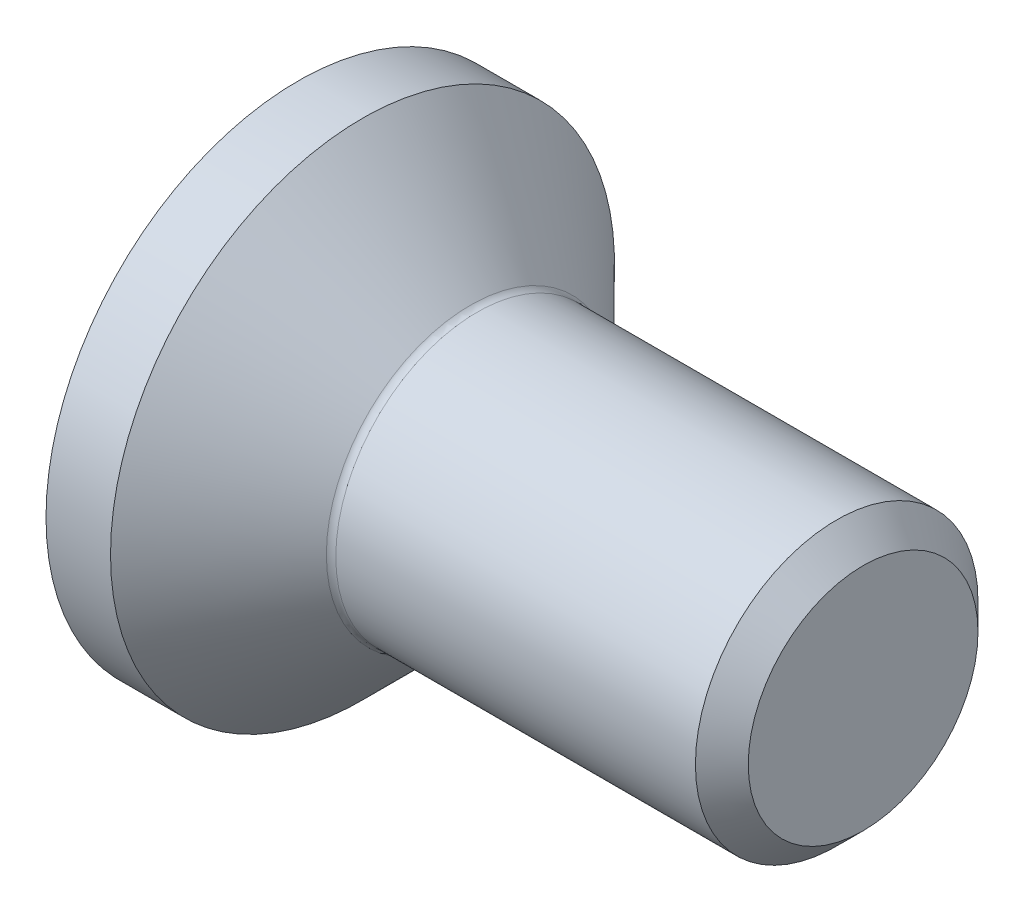
SolidWorks part; units mm, degrees
ref_plane "Plane1" through (0, 0, 0) normal (0, 0, 1) x (1, 0, 0)
ref_plane "Plane2" through (0, 0, 0) normal (0, 1, 0) x (1, 0, 0)
ref_plane "Plane3" through (0, 0, 0) normal (1, 0, 0) x (0, 0, -1)
revolve "BaseBody" add sketch "BodySke" angle 360 about L6
sketch "BodySke" plane through (0, 0, 0) normal (0, 0, 1) x (1, 0, 0)
  line L0 (0, 0) -> (0, 2.675)
  line L1 (0.685, 2.675) -> (1.86, 1.5)
  line L2 (0, 2.675) -> (0.685, 2.675)
  line L3 (1.86, 1.5) -> (5.7195, 1.5)
  line L4 (6, 1.2195) -> (6, 0)
  line L5 (6, 0) -> (0, 0)
  line L6 (0, 0) -> (127, 0) construction
  line L7 (0.685, -2.675) -> (1.86, -1.5) construction
  line L8 (6, 1.2195) -> (5.7195, 1.5)
  line L9 (0, -2.675) -> (0.685, -2.675) construction
  line L10 (6, -1.2195) -> (5.7195, -1.5) construction
  line L11 (2.36, 7.85) -> (2.36, -14.375) construction
  line L12 (0, 19.05) -> (0, -3.175) construction
  dimension "D1" = 0.685
  dimension "Diameter" = 3
  dimension "Head_ht" = 1.86
  dimension "Length" = 6
  dimension "Body_ch_ang" = 45
  dimension "Head_dia" = 5.35
  dimension "Minor_dia" = 2.439
  dimension "Head_ang" = 90
  dimension "Advance" = 0.5
  dimension "Thread_nom" = 6
cosmetic thread "ThreadCosmetic" [suppressed] parameters "Thread_length"=3.14, "Thread_minor"=2.439
fillet "Fillet1" radius 0.1 1 edges at (1.86, 0, 1.5)
sketch "Sketch2" plane through (0, 0, 0) normal (0, 0, 1) x (1, 0, 0)
  line L0 (0, 1) -> (1.1, 1)
  line L1 (1.1, 1) -> (1.6774, 0)
  line L2 (0, 0) -> (127, 0) construction
  line L3 (1.6774, 0) -> (0, 0)
  line L4 (0, 0) -> (0, 1)
  line L5 (0, -1) -> (1.1, -1) construction
  line L6 (0, 0) -> (47.625, 0) construction
  line L8 (0, 2.675) -> (0, -2.675) construction
  dimension "D2" = 60
  dimension "PreBroach_depth" = 1.1
  dimension "PreBroach_dia" = 2
revolve "PreBroach" cut sketch "Sketch2" angle 360 about L6
sketch "Sketch3" plane through (0, 0, 0) normal (-1, 0, 0) x (0, 0, 1)
  line L0 (-1, -0.5774) -> (-1, 0.5774)
  line L1 (-1, 0.5774) -> (0, 1.1547)
  line L2 (0, 1.1547) -> (1, 0.5774)
  line L3 (1, 0.5774) -> (1, -0.5774)
  line L4 (1, -0.5774) -> (0, -1.1547)
  line L5 (0, -1.1547) -> (-1, -0.5774)
  dimension "D1" = 1
  dimension "D2" = 1
  dimension "D3" = 2
  dimension "Hex_size" = 2
extrude "Hex" cut sketch "Sketch3" against normal blind 1.1
sketch "ThdSchSke" plane through (0, 0, 0) normal (0, 0, 1) x (1, 0, 0)
  line L0 (2.86, -1.2195) -> (2.6636, -1.5)
  line L1 (2.86, -1.2195) -> (3.0564, -1.5)
  line L2 (3.0564, -1.5) -> (3.0564, -1.875)
  line L3 (-3.175, 0) -> (5.1513, 0) construction
  line L4 (0, 2.675) -> (0, -2.675) construction
  line L5 (3.0564, -1.875) -> (2.6636, -1.875)
  line L6 (2.6636, -1.875) -> (2.6636, -1.5)
  dimension "Thread_minor" = 2.439
  dimension "Diameter" = 3
  dimension "Start" = 2.86
  dimension "SideAngle" = 55
  dimension "VeeAngle" = 70
  dimension "Overcut" = 3.75
revolve "ThreadSchematic" [suppressed] cut sketch "ThdSchSke" angle 360 about L3
pattern_linear "ThdSchPat" [suppressed]
equation "\"Thread_minor@ThreadCosmetic\"  =  \"Minor_dia@BodySke\""
equation "\"D1@Sketch3\" = \"Hex_size@Sketch3\" / 2"
equation "\"D2@Sketch3\" = \"D1@Sketch3\""
equation "\"D3@Sketch3\" = \"Hex_size@Sketch3\""
equation "\"Thread_length@ThreadCosmetic\" = ((sgn( (\"Length@BodySke\" - \"Advance@BodySke\" * 2.0 - \"Head_ht@BodySke\" ) - \"Thread_nom@BodySke\" )-1)*( (\"Length@BodySke\" - \"Advance@BodySke\" * 2.0 - \"Head_ht@BodySke\" ) - \"Thread_nom@BodySke\" ))/-2+ \"Thread_nom@BodySke\""
equation "\"Thread_minor@ThdSchSke\" = \"Minor_dia@BodySke\""
equation "\"Diameter@ThdSchSke\" = \"Diameter@BodySke\""
equation "\"Overcut@ThdSchSke\" = \"Diameter@BodySke\" * 1.25"
equation "\"Start@ThdSchSke\" = 0.000001 + \"Length@BodySke\" - \"Thread_length@ThreadCosmetic\"  '---Countersunk---"
equation "\"Num_threads@ThdSchPat\" = int( \"Thread_length@ThreadCosmetic\" / \"Advance@BodySke\" + 0.999 )  + 1"
equation "\"Advance@ThdSchPat\" = \"Thread_length@ThreadCosmetic\" /  (\"Num_threads@ThdSchPat\" - 1) 'relax it"
equation "\"Num_threads@ThdSchPat\" = \"Num_threads@ThdSchPat\" - sgn( \"Num_threads@ThdSchPat\" - 1) '---chamfered tips only---"
